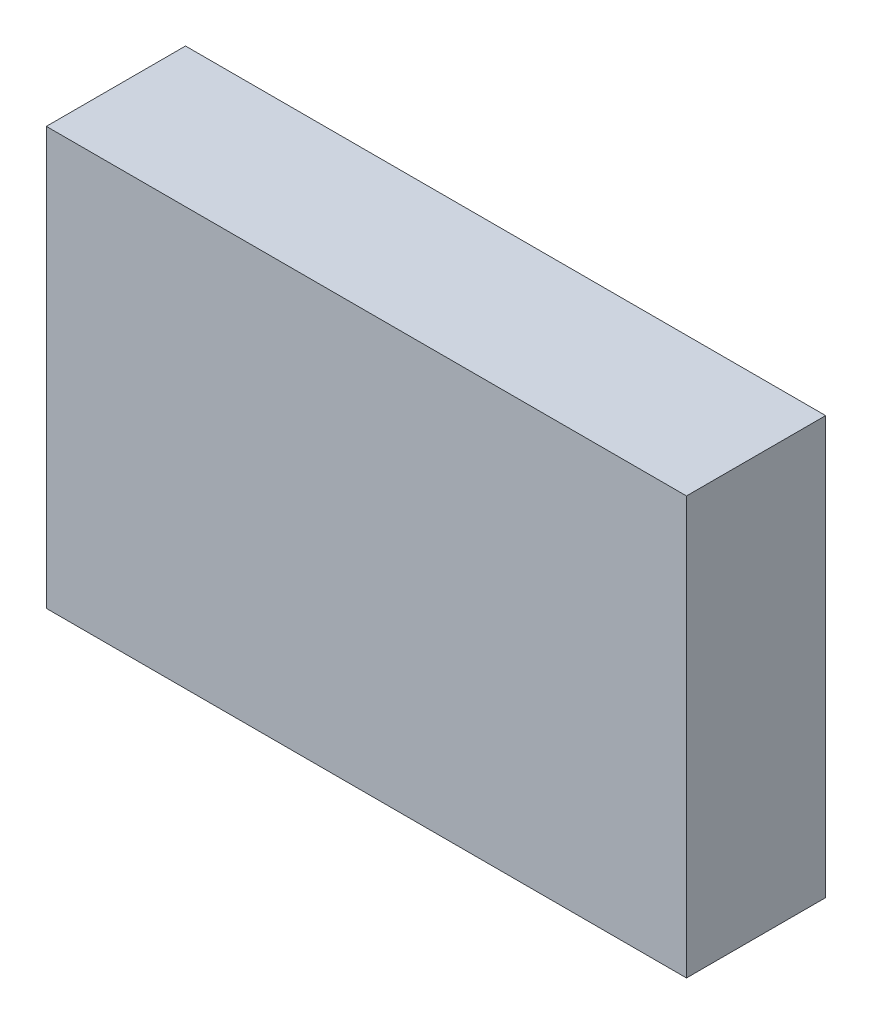
SolidWorks part; units mm, degrees
ref_plane "Plan de face" through (0, 0, 0) normal (0, 0, 1) x (1, 0, 0)
ref_plane "Plan de dessus" through (0, 0, 0) normal (0, 1, 0) x (1, 0, 0)
ref_plane "Plan de droite" through (0, 0, 0) normal (1, 0, 0) x (0, 0, -1)
sketch "Esquisse1" plane through (0, 0, 0) normal (0, 0, 1) x (1, 0, 0)
  line L0 (-23.0307, 0) -> (36.3914, 0) construction
  line L1 (-46, 30) -> (46, 30)
  line L2 (-46, 30) -> (-46, -30)
  line L3 (-46, -30) -> (46, -30)
  line L4 (46, 30) -> (46, -30)
  line L5 (0, 23.2736) -> (0, -21.7881) construction
  dimension "D1" = 60
  dimension "D2" = 92
extrude "Boss.-Extru.1" add sketch "Esquisse1" along normal blind 20
